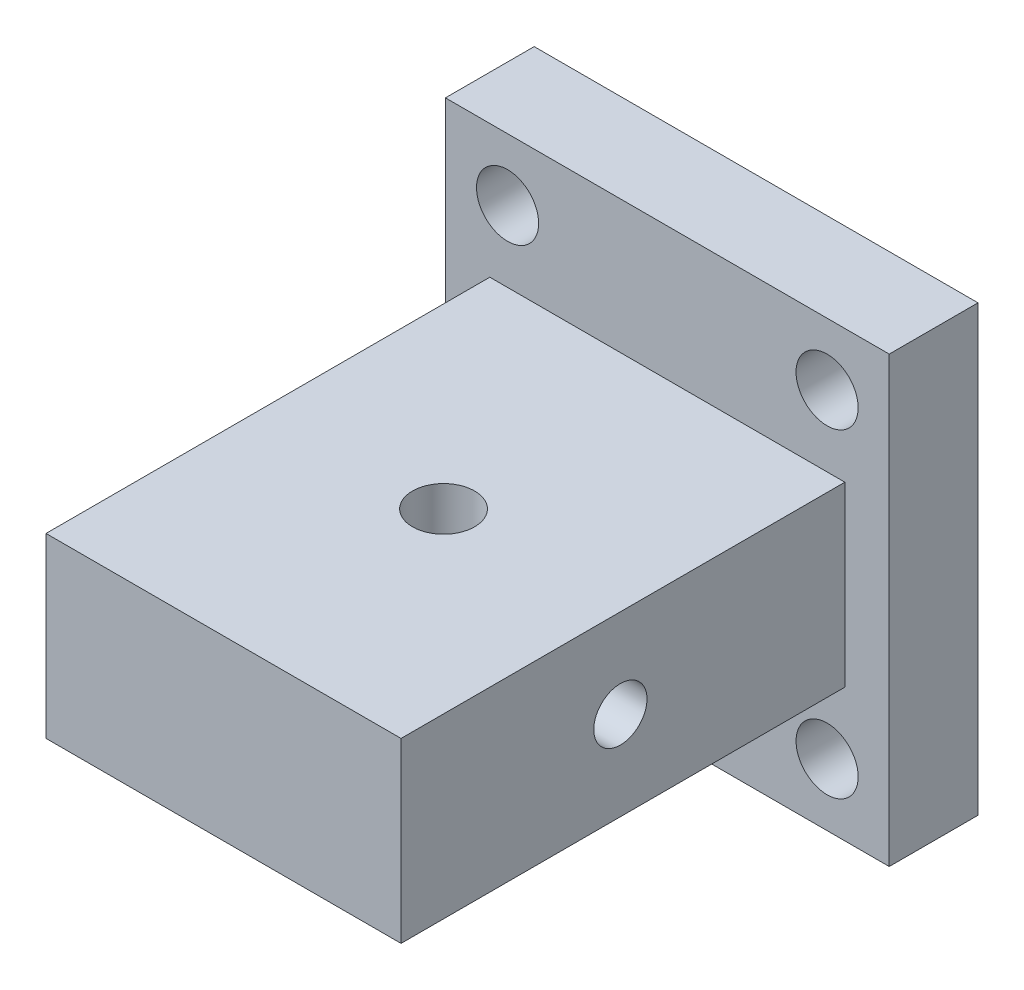
SolidWorks part; units mm, degrees
ref_plane "Front Plane" through (0, 0, 0) normal (0, 0, 1) x (1, 0, 0)
ref_plane "Top Plane" through (0, 0, 0) normal (0, 1, 0) x (1, 0, 0)
ref_plane "Right Plane" through (0, 0, 0) normal (1, 0, 0) x (0, 0, -1)
sketch "Sketch1" plane through (0, 0, 0) normal (0, 0, 1) x (1, 0, 0)
  line L1 (-25, -25) -> (25, -25)
  line L2 (-25, -25) -> (-25, 25)
  line L3 (-25, 25) -> (25, 25)
  line L4 (25, -25) -> (25, 25)
  line L5 (-25, -25) -> (25, 25) construction
  line L6 (-25, 25) -> (25, -25) construction
  point P0 (0, 0)
  dimension "D1" = 50
  dimension "D2" = 50
extrude "Boss-Extrude1" add sketch "Sketch1" along normal blind 10
sketch "Sketch2" plane through (0, 0, 10) normal (0, 0, 1) x (1, 0, 0)
  line L1 (-20, -10) -> (20, -10)
  line L2 (-20, -10) -> (-20, 10)
  line L3 (-20, 10) -> (20, 10)
  line L4 (20, -10) -> (20, 10)
  line L5 (-20, -10) -> (20, 10) construction
  line L6 (-20, 10) -> (20, -10) construction
  line L7 (-25, 25) -> (34.7935, 25) construction
  line L8 (-25, 25) -> (-19.3166, 25)
  line L11 (-25, 25) -> (-25, -25) construction
  line L12 (-25, 20.0207) -> (-25, 25)
  line L13 (-23, 14.8368) -> (-23, 31.1632) construction
  line L14 (-33.8548, 25.0103) -> (-15.0407, 25.0103) construction
  line L17 (0, 35.097) -> (0, -38.5294) construction
  line L18 (-35.2322, 0) -> (50.8622, 0) construction
  point P0 (0, 0)
  point P18 (-23, 23)
  dimension "D1" = 40
  dimension "D2" = 20
extrude "Boss-Extrude2" add sketch "Sketch2" along normal blind 50 contours L2 L1 L4 L3
sketch "Sketch3" plane through (0, 0, 10) normal (0, 0, 1) x (1, 0, 0)
  line L6 (25, 25) -> (-25, 25) construction
  line L7 (-25, 25) -> (-25, -25) construction
  line L8 (0, 25) -> (0, 38.5629) construction
  line L9 (0, 38.5629) -> (0, -35.2189) construction
  line L10 (-38.8189, 0) -> (36.5762, 0) construction
  circle A0 centre (-18, 18) radius 3.5
  circle A1 centre (18, 18) radius 3.5
  circle A2 centre (18, -18) radius 3.5
  circle A3 centre (-18, -18) radius 3.5
  dimension "D3" = 7
  dimension "D1" = 7
  dimension "D2" = 7
extrude "Cut-Extrude1" cut sketch "Sketch3" against normal blind 10
sketch "Sketch4" plane through (20, 0, 0) normal (1, 0, 0) x (0, 0, -1)
  line L0 (-64.0257, 0) -> (8.532, 0) construction
  line L1 (-35.29, 13.7474) -> (-35.29, -19.6252) construction
  circle A0 centre (-35.29, 0) radius 3
  dimension "D1" = 6
extrude "Cut-Extrude2" cut sketch "Sketch4" against normal through all
sketch "Sketch5" plane through (0, 10, 0) normal (0, 1, 0) x (1, 0, 0)
  line L0 (0, -7.9388) -> (0, -62.4844) construction
  line L1 (-23.511, -35) -> (28.4484, -35) construction
  circle A0 centre (0, -35.2116) radius 3.5
  dimension "D1" = 7
extrude "Cut-Extrude3" cut sketch "Sketch5" against normal blind 10
equation "\"length\" = 40mm"
equation "\"breadth\" = 20mm"
equation "\"height\"= 50mm"
equation "\"length base\" = 50mm"
equation "\"breadth base\"= 50mm"
equation "\"height base\"= 10mm"
equation "\"D1@Sketch1\"=\"breadth base\""
equation "\"D2@Sketch1\"=\"length base\""
equation "\"D1@Boss-Extrude1\"=\"height base\""
equation "\"D1@Sketch2\"=\"length\""
equation "\"D2@Sketch2\"=\"breadth\""
equation "\"D1@Boss-Extrude2\"=\"height\""
equation "\"hole\"= 7mm"
equation "\"hole distance from edge\"= 7mm"
equation "\"D3@Sketch3\"=\"hole\""
equation "\"D1@Sketch3\"=\"hole distance from edge\""
equation "\"D2@Sketch3\"=\"hole distance from edge\""
equation "\"D1@Cut-Extrude1\"=\"height base\""
equation "\"D1@Sketch5\"=\"hole\""
